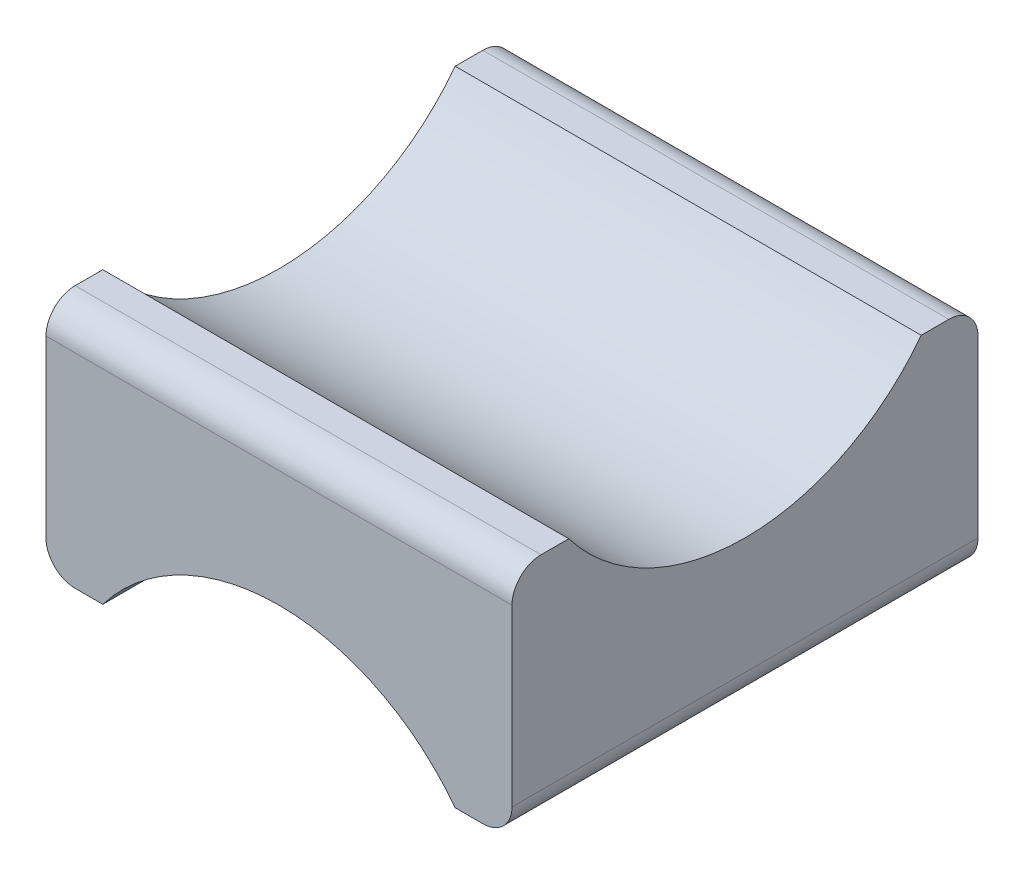
SolidWorks part; units mm, degrees
ref_plane "Front Plane" through (0, 0, 0) normal (0, 0, 1) x (1, 0, 0)
ref_plane "Top Plane" through (0, 0, 0) normal (0, 1, 0) x (1, 0, 0)
ref_plane "Right Plane" through (0, 0, 0) normal (1, 0, 0) x (0, 0, -1)
sketch "Sketch1" plane through (0, 0, 0) normal (0, 0, 1) x (1, 0, 0)
  line L0 (8, 4) -> (-8, -4) construction
  line L1 (8, 4) -> (-8, 4)
  line L2 (8, 4) -> (8, -4)
  line L3 (8, -4) -> (6.0498, -4)
  line L4 (-8, 4) -> (-8, -4)
  line L5 (-6.0498, -4) -> (-8, -4)
  arc A0 (6.0498, -4) -> (-6.0498, -4) centre (0, -8.6) ccw
  point P4 (0, -1)
  point P8 (0, -8.0447)
  point P9 (9, -5.7142)
  point P11 (0, 0)
  dimension "D1" = 15.2
  dimension "D2" = 1
  dimension "D3" = 16
  dimension "D4" = 3
extrude "Boss-Extrude1" add sketch "Sketch1" along normal mid plane 16
sketch "Sketch2" plane through (-8, 0, 0) normal (-1, 0, 0) x (0, 0, 1)
  circle A0 centre (0, 8.6) radius 7.6
  point P3 (0, 1)
  dimension "D1" = 15.2
  dimension "D2" = 1
extrude "Cut-Extrude1" cut sketch "Sketch2" against normal blind 26
fillet "Fillet1" radius 1 4 edges at (-8, -4, 0) (8, -4, 0) (0, 4, 8) (0, 4, -8)
